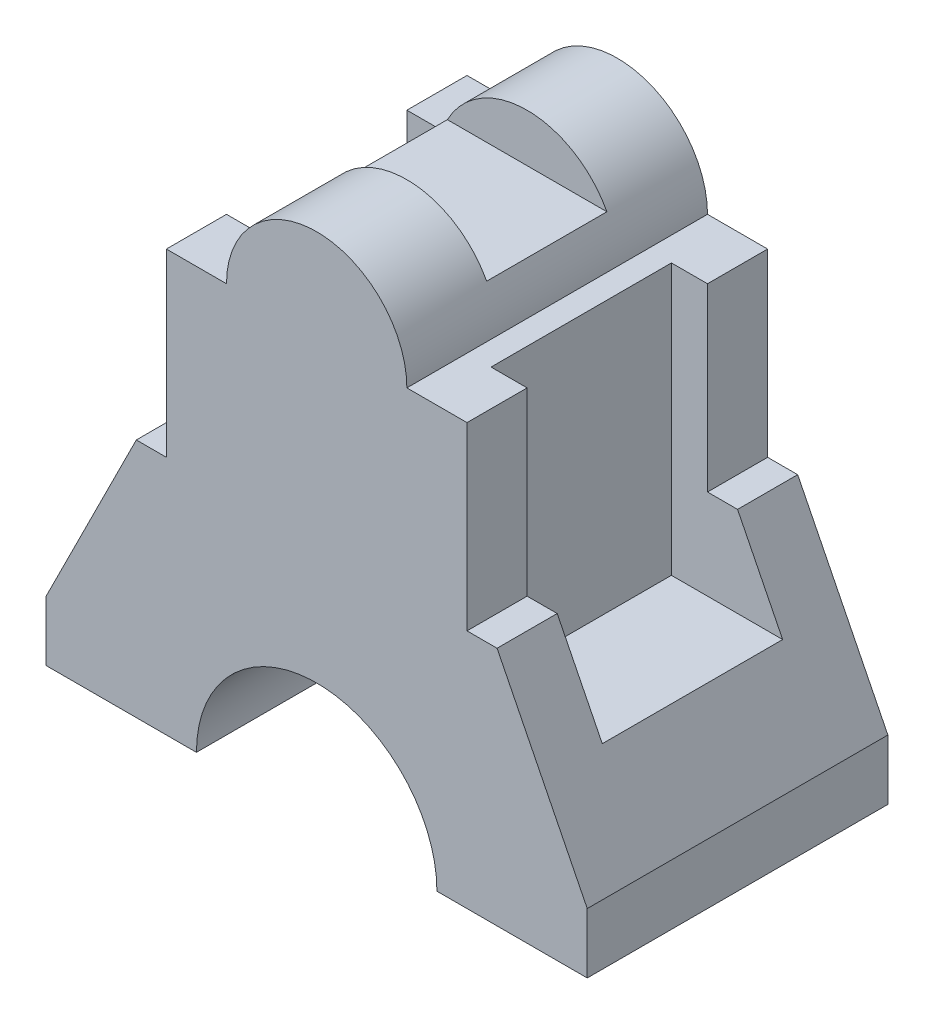
SolidWorks part; units mm, degrees
ref_plane "Front Plane" through (0, 0, 0) normal (0, 0, 1) x (1, 0, 0)
ref_plane "Top Plane" through (0, 0, 0) normal (0, 1, 0) x (1, 0, 0)
ref_plane "Right Plane" through (0, 0, 0) normal (1, 0, 0) x (0, 0, -1)
sketch "Sketch3" plane through (0, 0, 0) normal (0, 0, 1) x (1, 0, 0)
  line L0 (45, 0) -> (-45, 0)
  line L1 (-45, 0) -> (-45, 10)
  line L2 (-45, 10) -> (-30, 40)
  line L3 (0, 0) -> (0, 40)
  line L4 (30, 40) -> (-30, 40)
  line L5 (0, 40) -> (0, 70)
  line L6 (25, 70) -> (-25, 70)
  line L7 (-25, 70) -> (-25, 40)
  line L8 (-25, 40) -> (25, 40)
  line L9 (0, 85) -> (0, 70)
  line L10 (-15, 70) -> (15, 70)
  line L11 (0, 6.2073) -> (0, -6.2073) construction
  line L12 (45, 0) -> (45, 10)
  line L13 (45, 10) -> (30, 40)
  line L14 (25, 70) -> (25, 40)
  arc A0 (-15, 70) -> (15, 70) centre (0, 70) cw
  dimension "D3" = 15
  dimension "D1" = 45
  dimension "D2" = 10
  dimension "D4" = 25
  dimension "D5" = 30
extrude "Boss-Extrude2" add sketch "Sketch3" along normal mid plane 50 contours A0 L6 L9 | A0 L9 L6 | L14 L6 L5 L4 | L3 L4 L2 L1 L0 | L12 L13 L4 L3 L0 | L6 L7 L4 L5
sketch "Sketch6" plane through (0, 0, 0) normal (1, 0, 0) x (0, 0, -1)
  line L1 (-10, 85) -> (10, 85)
  line L2 (-10, 85) -> (-10, 77)
  line L3 (-10, 77) -> (10, 77)
  line L4 (10, 85) -> (10, 77)
  line L5 (-10, 85) -> (10, 77) construction
  line L6 (-10, 77) -> (10, 85) construction
  point P0 (0, 81)
  dimension "D1" = 20
  dimension "D2" = 8
  dimension "D3" = 77
extrude "Cut-Extrude1" cut sketch "Sketch6" against normal mid plane 50
sketch "Sketch7" plane through (0, 0, -25) normal (0, 0, -1) x (-1, 0, 0)
  line L0 (-45, 0) -> (45, 0) construction
  line L1 (-20, 0) -> (20, 0)
  arc A0 (-20, 0) -> (20, 0) centre (0, 0) cw
  dimension "D1" = 20
extrude "Cut-Extrude2" cut sketch "Sketch7" against normal through all
ref_plane "Plane1" through (0, 70, 0) normal (0, 1, 0) x (1, 0, 0)
sketch "Sketch11" plane through (0, 70, 0) normal (0, 1, 0) x (1, 0, 0)
  line L0 (-45, -25) -> (-45, 25) construction
  line L1 (-19, -15) -> (-45, -15)
  line L2 (-19, -15) -> (-19, 15)
  line L3 (-19, 15) -> (-45, 15)
  line L4 (-45, -15) -> (-45, 15)
  line L5 (0, -51.1951) -> (0, 50.8909) construction
  line L6 (19, 15) -> (45, 15)
  line L7 (45, -15) -> (45, 15)
  line L8 (19, -15) -> (45, -15)
  line L9 (19, -15) -> (19, 15)
  dimension "D1" = 19
  dimension "D2" = 15
  dimension "D3" = 15
extrude "Cut-Extrude3" cut sketch "Sketch11" against normal blind 45
